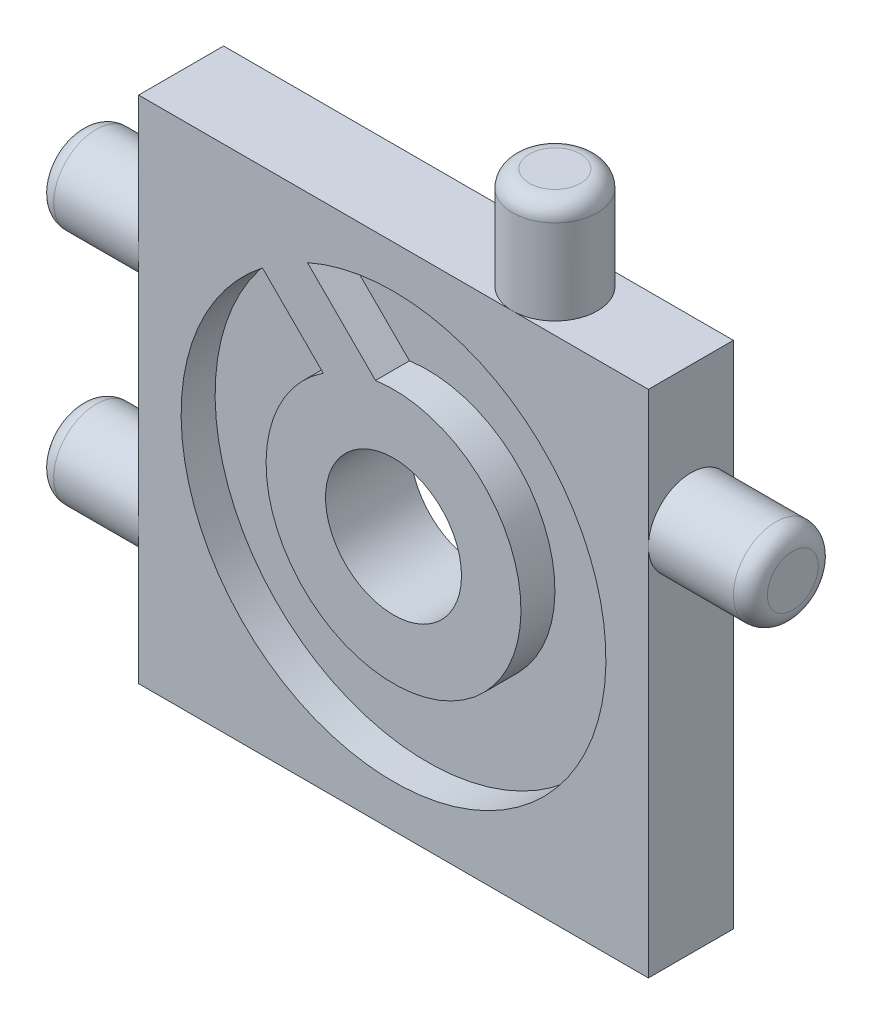
SolidWorks part; units mm, degrees
ref_plane "Plan de face" through (0, 0, 0) normal (0, 0, 1) x (1, 0, 0)
ref_plane "Plan de dessus" through (0, 0, 0) normal (0, 1, 0) x (1, 0, 0)
ref_plane "Plan de droite" through (0, 0, 0) normal (1, 0, 0) x (0, 0, -1)
sketch "Esquisse2" plane through (0, 0, 0) normal (0, 0, 1) x (1, 0, 0)
  line L1 (-15, 15) -> (15, 15)
  line L2 (-15, 15) -> (-15, -15)
  line L3 (-15, -15) -> (15, -15)
  line L4 (15, 15) -> (15, -15)
  line L5 (-15, 15) -> (15, -15) construction
  line L6 (-15, -15) -> (15, 15) construction
  point P0 (0, 0)
  dimension "D1" = 30
  dimension "D2" = 30
extrude "Boss.-Extru.1" add sketch "Esquisse2" along normal blind 5 contours L1 L4 L3 L2
sketch "Esquisse8" plane through (0, 0, 5) normal (0, 0, 1) x (1, 0, 0)
  circle A0 centre (0, 0) radius 12.5
  dimension "D1" = 25
sketch "Esquisse16" plane through (-15, 0, 0) normal (-1, 0, 0) x (0, 0, 1)
  line L0 (2.5, 15) -> (2.5, -15) construction
  line L1 (5, 15) -> (0, 15) construction
  line L2 (5, -15) -> (0, -15) construction
  circle A0 centre (2.5, 7) radius 2.5
  circle A1 centre (2.5, -7) radius 2.5
  dimension "D3" = 5
  dimension "D4" = 5
  dimension "D1" = 8
  dimension "D2" = 8
extrude "Boss.-Extru.7" add sketch "Esquisse16" along normal blind 6
fillet "Congé3" radius 1 2 edges at (-21, -9.5, 2.5) (-21, 4.5, 2.5)
sketch "Esquisse18" plane through (15, 0, 0) normal (1, 0, 0) x (0, 0, -1)
  line L0 (-2.5, -15) -> (-2.5, 15) construction
  line L1 (-5, -15) -> (0, -15) construction
  line L2 (-5, 15) -> (0, 15) construction
  circle A0 centre (-2.5, 7) radius 2.5
  dimension "D2" = 5
  dimension "D1" = 8
extrude "Boss.-Extru.9" add sketch "Esquisse18" along normal blind 6
fillet "Congé5" radius 1 1 edges at (21, 9.5, 2.5)
extrude "Enlèv. mat.-Extru.1" cut sketch "Esquisse8" against normal blind 2 contours A0
sketch "Esquisse19" plane through (0, 0, 3) normal (0, 0, 1) x (1, 0, 0)
  circle A0 centre (0, 0) radius 7.5
  dimension "D1" = 15
extrude "Boss.-Extru.10" add sketch "Esquisse19" along normal blind 2
sketch "Esquisse31" plane through (0, 0, 3) normal (0, 0, 1) x (1, 0, 0)
  line L0 (-15, 15) -> (15, -15) construction
  line L1 (15, 15) -> (-15, -15) construction
  line L2 (-8.1317, 10.253) -> (-6.0104, 12.3744)
  line L3 (-3.182, 5.3033) -> (-1.0607, 7.4246)
  line L4 (-8.1317, 10.253) -> (-3.182, 5.3033)
  line L6 (-6.0104, 12.3744) -> (-1.0607, 7.4246)
  dimension "D1" = 3
  dimension "D2" = 6
  dimension "D3" = 7
  dimension "D4" = 1.5
sketch "Esquisse33" plane through (0, 0, 5) normal (0, 0, 1) x (1, 0, 0)
  circle A0 centre (0, 0) radius 4
extrude "Enlèv. mat.-Extru.3" cut sketch "Esquisse33" against normal through all
sketch "Esquisse35" plane through (0, 15, 0) normal (0, 1, 0) x (1, 0, 0)
  line L0 (-15, -2.5) -> (15, -2.5) construction
  line L1 (-15, -5) -> (-15, 0) construction
  line L2 (15, -5) -> (15, 0) construction
  circle A0 centre (7, -2.5) radius 2.5
  dimension "D1" = 8
extrude "Boss.-Extru.26" add sketch "Esquisse35" along normal blind 6
fillet "Congé6" radius 1 1 edges at (7, 21, 5)
extrude "Boss.-Extru.27" add sketch "Esquisse31" along normal blind 2 and the other way blind 5.5 contours L4 L3 L6 L2
